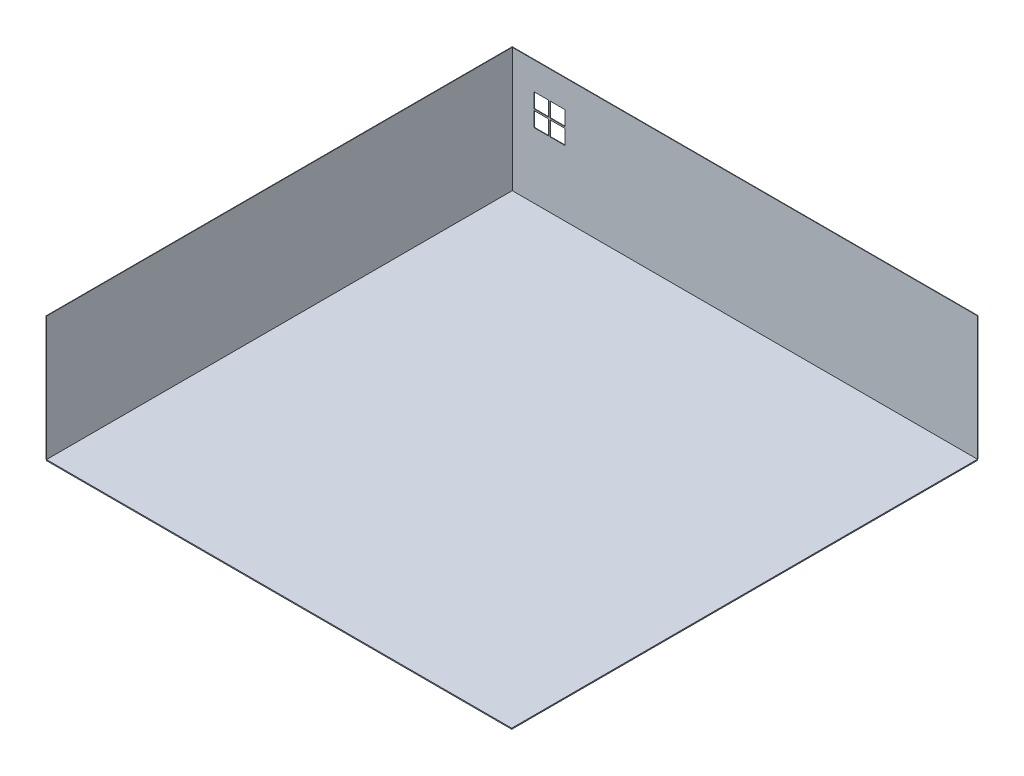
SolidWorks part; units mm, degrees
ref_plane "Front Plane" through (0, 0, 0) normal (0, 0, 1) x (1, 0, 0)
ref_plane "Top Plane" through (0, 0, 0) normal (0, 1, 0) x (1, 0, 0)
ref_plane "Right Plane" through (0, 0, 0) normal (1, 0, 0) x (0, 0, -1)
sketch "Sketch1" plane through (0, 0, 0) normal (0, 1, 0) x (1, 0, 0)
  line L1 (0, 0) -> (-10, 0)
  line L2 (0, 0) -> (0, 9144)
  line L3 (0, 9144) -> (-10, 9144)
  line L4 (-10, 0) -> (-10, 9144)
  line L5 (-10, 9144) -> (9134, 9144)
  line L6 (-10, 9144) -> (-10, 9154)
  line L7 (-10, 9154) -> (9134, 9154)
  line L8 (9134, 9144) -> (9134, 9154)
  dimension "D1" = 9144
  dimension "D2" = 10
  dimension "D3" = 10
  dimension "D4" = 9144
extrude "Boss-Extrude1" add sketch "Sketch1" along normal blind 2438.4 contours L4 L1 L2 L3 | L6 L7 L8 L5
sketch "Sketch3" plane through (0, 0, -9144) normal (0, 0, 1) x (1, 0, 0)
  line L0 (422.9628, 1590.4097) -> (727.7628, 1590.4097)
  line L1 (422.9628, 1285.6097) -> (1032.5628, 1285.6097)
  line L2 (422.9628, 1285.6097) -> (422.9628, 1895.2097)
  line L3 (422.9628, 1895.2097) -> (1032.5628, 1895.2097)
  line L4 (1032.5628, 1285.6097) -> (1032.5628, 1895.2097)
  line L5 (422.9628, 1575.4097) -> (727.7628, 1575.4097)
  line L6 (742.7628, 1590.4097) -> (742.7628, 1895.2097)
  line L7 (727.7628, 1590.4097) -> (727.7628, 1895.2097)
  line L8 (727.7628, 1590.4097) -> (1032.5628, 1590.4097)
  line L9 (727.7628, 1590.4097) -> (727.7628, 1285.6097)
  line L10 (727.7628, 1575.4097) -> (1032.5628, 1575.4097)
  line L11 (712.7628, 1590.4097) -> (712.7628, 1285.6097)
  line L12 (422.9628, 1605.4097) -> (727.7628, 1605.4097)
  line L13 (712.7628, 1590.4097) -> (712.7628, 1895.2097)
  line L14 (727.7628, 1605.4097) -> (1032.5628, 1605.4097)
  line L15 (742.7628, 1590.4097) -> (742.7628, 1285.6097)
  point P0 (727.7628, 1590.4097)
  dimension "D1" = 609.6
  dimension "D2" = 15
  dimension "D3" = 15
extrude "Cut-Extrude1" cut sketch "Sketch3" against normal through all contours L12 L13 L3 L2 | L6 L14 L4 L3 | L10 L15 L1 L4 | L11 L5 L2 L1
sketch "Sketch4" plane through (0, 0, 0) normal (0, -1, 0) x (1, 0, 0)
  line L1 (-10, 0) -> (9134, 0)
  line L2 (-10, 0) -> (-10, -9144)
  line L3 (-10, -9144) -> (9134, -9144)
  line L4 (9134, 0) -> (9134, -9144)
  line M4 (9134, -9144) -> (0, -9144)
  line M5 (0, -9144) -> (0, 0)
extrude "Boss-Extrude3" add sketch "Sketch4" along normal blind 20 separate body contours L4 L1 M5 M4
